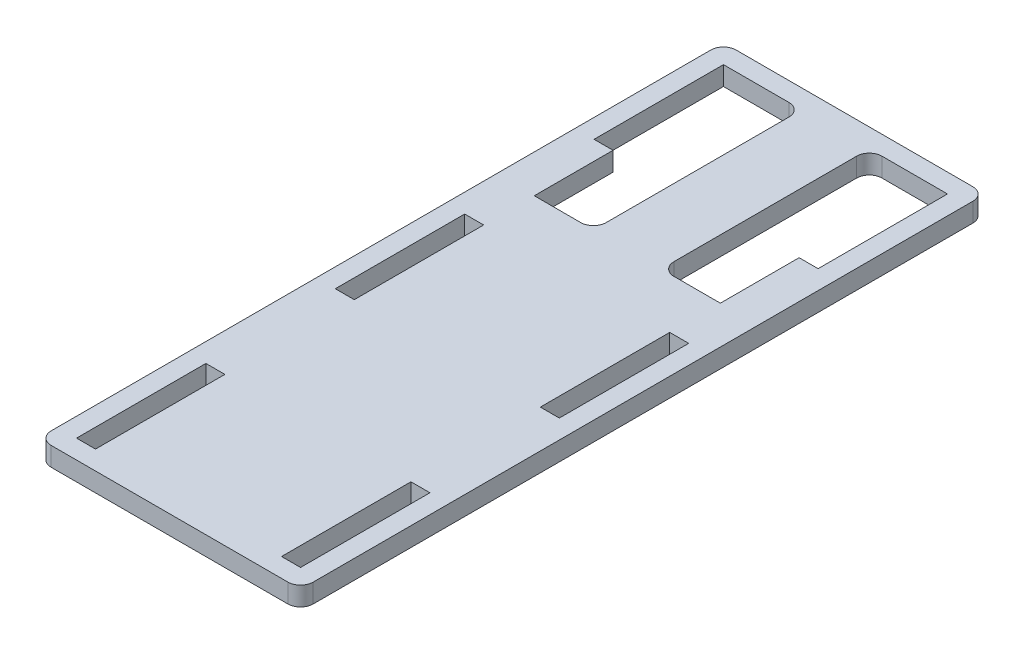
SolidWorks part; units mm, degrees
ref_plane "Front Plane" through (0, 0, 0) normal (0, 0, 1) x (1, 0, 0)
ref_plane "Top Plane" through (0, 0, 0) normal (0, 1, 0) x (1, 0, 0)
ref_plane "Right Plane" through (0, 0, 0) normal (1, 0, 0) x (0, 0, -1)
sketch "Sketch1" plane through (0, 0, 0) normal (0, 1, 0) x (1, 0, 0)
  line L0 (-14.7, 0) -> (14.7, 0) construction
  line L1 (-20.7, -54.112) -> (20.7, -54.112)
  line L2 (-20.7, -54.112) -> (-20.7, 54.112)
  line L3 (-20.7, 54.112) -> (20.7, 54.112)
  line L4 (20.7, -54.112) -> (20.7, 54.112)
  line L5 (-20.7, -54.112) -> (20.7, 54.112) construction
  line L6 (-20.7, 54.112) -> (20.7, -54.112) construction
  line L7 (14.7, 30.6672) -> (17.7, 30.6672)
  line L8 (14.7, 30.6672) -> (14.7, 51.112)
  line L9 (14.7, 51.112) -> (17.7, 51.112)
  line L10 (17.7, 30.6672) -> (17.7, 51.112)
  line L11 (14.7, 30.6672) -> (17.7, 51.112) construction
  line L12 (14.7, 51.112) -> (17.7, 30.6672) construction
  line L13 (14.7, -10.2224) -> (17.7, -10.2224)
  line L14 (14.7, -10.2224) -> (14.7, 10.2224)
  line L15 (14.7, 10.2224) -> (17.7, 10.2224)
  line L16 (17.7, -10.2224) -> (17.7, 10.2224)
  line L17 (14.7, -10.2224) -> (17.7, 10.2224) construction
  line L18 (14.7, 10.2224) -> (17.7, -10.2224) construction
  line L19 (14.7, -51.112) -> (17.7, -51.112)
  line L20 (14.7, -51.112) -> (14.7, -30.6672)
  line L21 (14.7, -30.6672) -> (17.7, -30.6672)
  line L22 (17.7, -51.112) -> (17.7, -30.6672)
  line L23 (14.7, -51.112) -> (17.7, -30.6672) construction
  line L24 (14.7, -30.6672) -> (17.7, -51.112) construction
  line L25 (-17.7, -51.112) -> (-14.7, -51.112)
  line L26 (-17.7, -51.112) -> (-17.7, -30.6672)
  line L27 (-17.7, -30.6672) -> (-14.7, -30.6672)
  line L28 (-14.7, -51.112) -> (-14.7, -30.6672)
  line L29 (-17.7, -51.112) -> (-14.7, -30.6672) construction
  line L30 (-17.7, -30.6672) -> (-14.7, -51.112) construction
  line L31 (-17.7, -10.2224) -> (-14.7, -10.2224)
  line L32 (-17.7, -10.2224) -> (-17.7, 10.2224)
  line L33 (-17.7, 10.2224) -> (-14.7, 10.2224)
  line L34 (-14.7, -10.2224) -> (-14.7, 10.2224)
  line L35 (-17.7, -10.2224) -> (-14.7, 10.2224) construction
  line L36 (-17.7, 10.2224) -> (-14.7, -10.2224) construction
  line L37 (-17.7, 30.6672) -> (-14.7, 30.6672)
  line L38 (-17.7, 30.6672) -> (-17.7, 51.112)
  line L39 (-17.7, 51.112) -> (-14.7, 51.112)
  line L40 (-14.7, 30.6672) -> (-14.7, 51.112)
  line L41 (-17.7, 30.6672) -> (-14.7, 51.112) construction
  line L42 (-17.7, 51.112) -> (-14.7, 30.6672) construction
  line L43 (-14.7, 30.6672) -> (-14.7, 10.2224) construction
  line L44 (-14.7, -10.2224) -> (-14.7, -30.6672) construction
  line L45 (17.7, 54.112) -> (17.7, 51.112) construction
  line L46 (17.7, 51.112) -> (20.7, 51.112) construction
  line L47 (-20.7, -51.112) -> (-17.7, -51.112) construction
  line L48 (-17.7, -51.112) -> (-17.7, -54.112) construction
  point P0 (0, 0)
  point P6 (16.2, 40.8896)
  point P11 (16.2, 0)
  point P16 (16.2, -40.8896)
  point P21 (-16.2, -40.8896)
  point P26 (-16.2, 0)
  point P31 (-16.2, 40.8896)
  point P41 (0, 0)
  dimension "D1" = 3
  dimension "D2" = 20.4448
  dimension "D3" = 29.4
extrude "Boss-Extrude1" add sketch "Sketch1" along normal blind 3
sketch "Sketch2" plane through (0, 3, 0) normal (0, 1, 0) x (1, 0, 0)
  line L0 (-14.7, 51.112) -> (14.7, 51.112)
  line L2 (14.7, 51.112) -> (14.7, 18.2224)
  line L3 (14.7, 18.2224) -> (-14.7, 18.2224)
  line L4 (-14.7, 18.2224) -> (-14.7, 51.112)
  line L5 (-14.7, 10.2224) -> (-17.7, 10.2224) construction
  line L10 (-5.35, 18.2224) -> (5.35, 18.2224)
  line L11 (-5.35, 18.2224) -> (-5.35, 51.112)
  line L12 (-5.35, 51.112) -> (5.35, 51.112)
  line L13 (5.35, 18.2224) -> (5.35, 51.112)
  line L14 (-5.35, 18.2224) -> (5.35, 51.112) construction
  line L15 (-5.35, 51.112) -> (5.35, 18.2224) construction
  point P3 (0, 0)
  point P10 (0, 34.6672)
  point P16 (0, 0)
  line M13 (14.7, 30.6672) -> (14.7, 51.112)
  line M27 (-14.7, 51.112) -> (-14.7, 30.6672)
  dimension "D1" = 8
  dimension "D2" = 10.7
extrude "Cut-Extrude1" cut sketch "Sketch2" against normal through all both and the other way through all contours L3 L11 L0 L4 M27 | L13 L3 L2 L0 M13
fillet "Fillet1" radius 2 8 edges at (-20.7, 1.5, 54.112) (20.7, 1.5, 54.112) (20.7, 1.5, -54.112) (-20.7, 1.5, -54.112) (-5.35, 1.5, -51.112) (-5.35, 1.5, -18.2224) (5.35, 1.5, -18.2224) (5.35, 1.5, -51.112)
